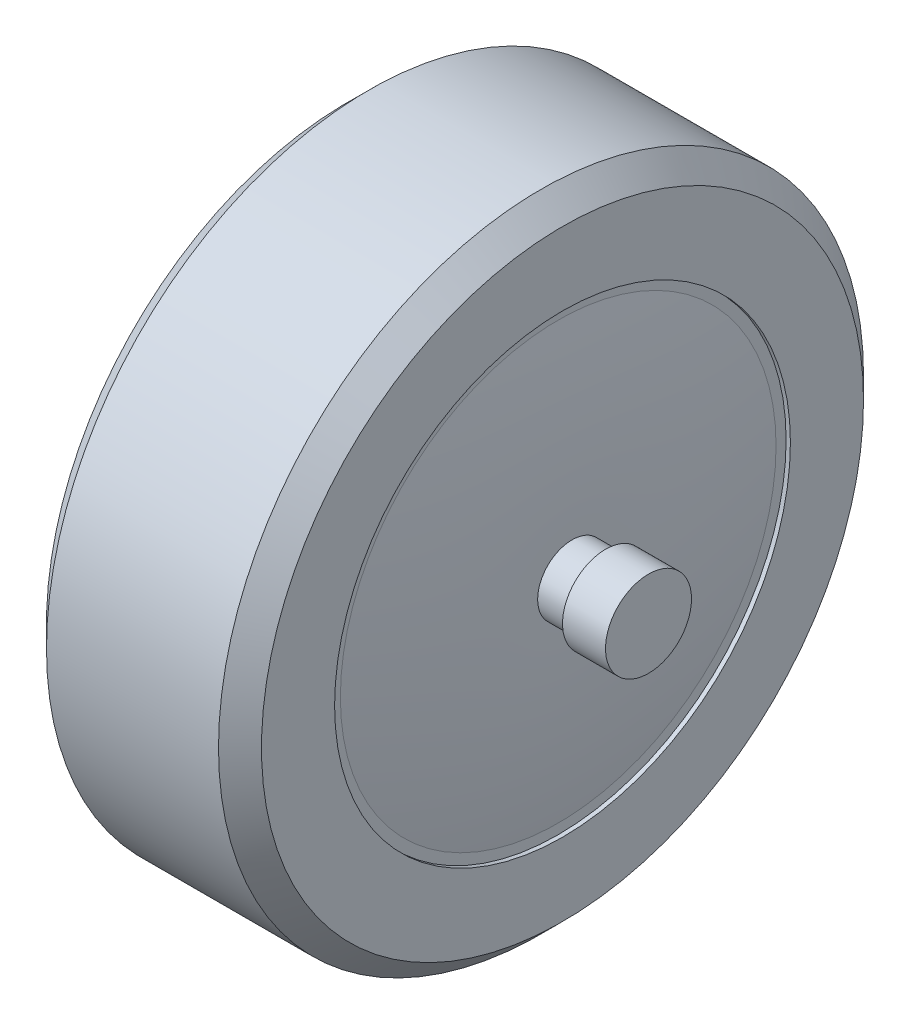
SolidWorks part; units mm, degrees
ref_plane "Front Plane" through (0, 0, 0) normal (0, 0, 1) x (1, 0, 0)
ref_plane "Top Plane" through (0, 0, 0) normal (0, 1, 0) x (1, 0, 0)
ref_plane "Right Plane" through (0, 0, 0) normal (1, 0, 0) x (0, 0, -1)
sketch "Sketch1" plane through (0, 0, 0) normal (1, 0, 0) x (0, 0, -1)
  circle A0 centre (0, 0) radius 75
extrude "Boss-Extrude1" add sketch "Sketch1" along normal mid plane 50
sketch "Sketch2" plane through (0, 0, 0) normal (1, 0, 0) x (0, 0, -1)
  circle A0 centre (0, 0) radius 8
extrude "Boss-Extrude2" add sketch "Sketch2" along normal mid plane 70
sketch "Sketch3" plane through (35, 0, 0) normal (1, 0, 0) x (0, 0, -1)
  circle A0 centre (0, 0) radius 10
extrude "Boss-Extrude3" add sketch "Sketch3" along normal blind 10
mirror "Mirror1" about plane through (0, 0, 0) normal (1, 0, 0) of "Boss-Extrude3"
chamfer "Chamfer1" distance 5 angle 45 2 edges at (-25, 0, -75) (25, 0, -75)
sketch "Sketch4" plane through (25, 0, 0) normal (1, 0, 0) x (0, 0, -1)
  circle A0 centre (0, 0) radius 8 construction
  circle A1 centre (0, 0) radius 8
  circle A2 centre (0, 0) radius 53
  dimension "D1" = 45
extrude "Cut-Extrude1" cut sketch "Sketch4" against normal blind 1
mirror "Mirror2" about plane through (0, 0, 0) normal (1, 0, 0) of "Cut-Extrude1"
sketch "Sketch5" plane through (0, 0, 0) normal (0, 1, 0) x (1, 0, 0)
  line L0 (24, 0) -> (24, 50.6612)
  line L1 (24, -8) -> (24, 8) construction
  line L2 (24, 0) -> (27, 0)
  line L3 (27, 0) -> (35.0988, 0) construction
  spline S0 degree 2 poles (27, 0) (28.0996, 25.4639) (24, 50.6612) knots 0 0 0 1 1 1
revolve "Revolve1" add sketch "Sketch5" angle 360 about L3
mirror "Mirror3" about plane through (0, 0, 0) normal (1, 0, 0) of "Revolve1"
